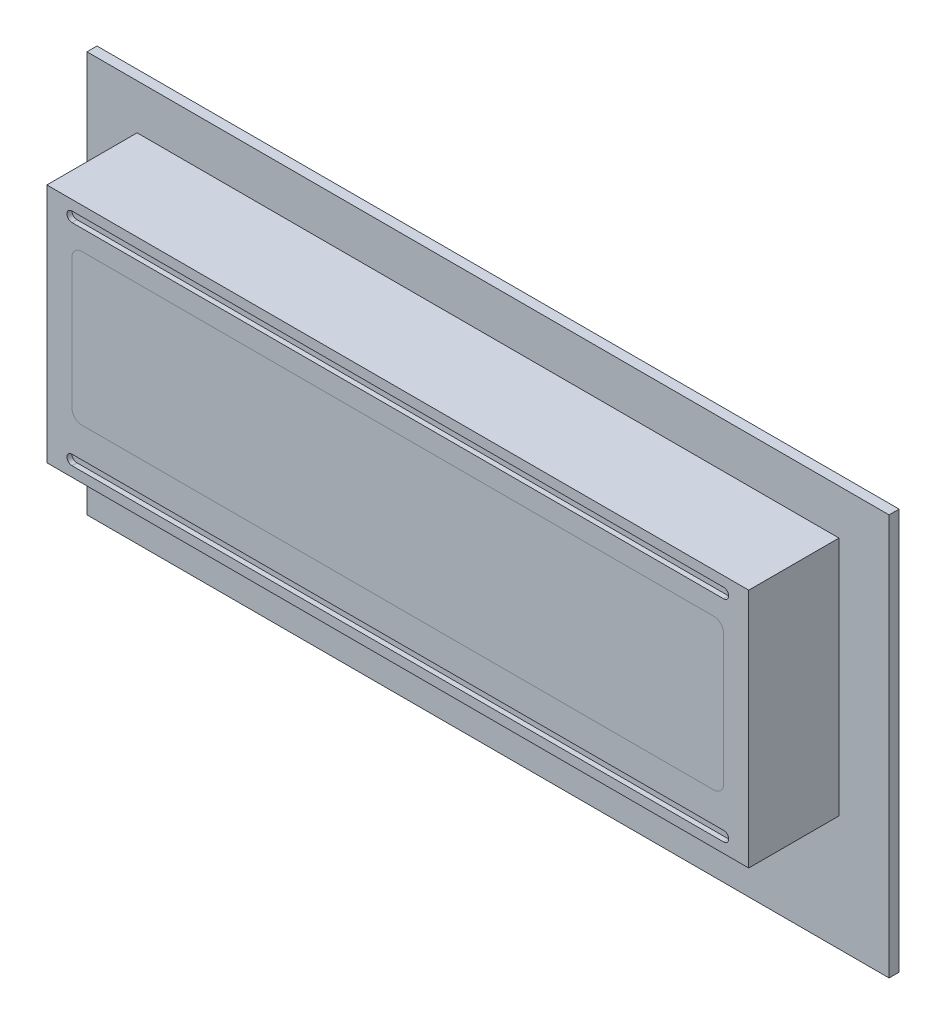
SolidWorks part; units mm, degrees
ref_plane "Plan de face" through (0, 0, 0) normal (0, 0, 1) x (1, 0, 0)
ref_plane "Plan de dessus" through (0, 0, 0) normal (0, 1, 0) x (1, 0, 0)
ref_plane "Plan de droite" through (0, 0, 0) normal (1, 0, 0) x (0, 0, -1)
sketch "Esquisse1" plane through (0, 0, 0) normal (0, 0, 1) x (1, 0, 0)
  line L0 (0, 30.9281) -> (0, -19.2371) construction
  line L1 (-46.5895, 0) -> (45.4509, 0) construction
  line L2 (-40, 20) -> (40, 20)
  line L3 (-40, 20) -> (-40, -20)
  line L4 (-40, -20) -> (40, -20)
  line L5 (40, 20) -> (40, -20)
  dimension "D1" = 80
  dimension "D2" = 40
extrude "Boss.-Extru.1" add sketch "Esquisse1" along normal blind 1
sketch "Esquisse2" plane through (0, 0, 1) normal (0, 0, 1) x (1, 0, 0)
  line L0 (0, -23.7129) -> (0, 24.4015) construction
  line L1 (-35, 15.5) -> (35, 15.5)
  line L2 (-35, 15.5) -> (-35, -8.5)
  line L3 (-35, -8.5) -> (35, -8.5)
  line L4 (35, 15.5) -> (35, -8.5)
  line L5 (-31.5, 11.5) -> (31.5, 11.5)
  line L6 (-32.5, 10.5) -> (-32.5, -2.5)
  line L7 (-31.5, -3.5) -> (31.5, -3.5)
  line L8 (32.5, 10.5) -> (32.5, -2.5)
  line L9 (40, 20) -> (-40, 20) construction
  arc A0 (31.5, -3.5) -> (32.5, -2.5) centre (31.5, -2.5) ccw
  arc A1 (31.5, 11.5) -> (32.5, 10.5) centre (31.5, 10.5) cw
  arc A2 (-32.5, -2.5) -> (-31.5, -3.5) centre (-31.5, -2.5) ccw
  arc A3 (-31.5, 11.5) -> (-32.5, 10.5) centre (-31.5, 10.5) ccw
  dimension "D7" = 1
  dimension "D1" = 70
  dimension "D2" = 24
  dimension "D3" = 4
  dimension "D4" = 15
  dimension "D5" = 65
  dimension "D6" = 4.5
extrude "Boss.-Extru.2" add sketch "Esquisse2" along normal blind 9
sketch "Esquisse3" plane through (0, 0, 10) normal (0, 0, 1) x (1, 0, 0)
  line L0 (0, -23.3686) -> (0, 26.295) construction
  line L2 (-32.5, 14.5) -> (32.5, 14.5)
  line L3 (-32.5, 13.2271) -> (-32.5, 14.6724) construction
  line L4 (-32.5, 13.5) -> (32.5, 13.5)
  line L5 (32.5, 13.1751) -> (32.5, 14.8249) construction
  line L6 (31.5, 11.5) -> (-31.5, 11.5) construction
  line L7 (-44.4775, 3.5) -> (44.11, 3.5) construction
  line L8 (35, 15.5) -> (-35, 15.5) construction
  line L9 (-35, -8.5) -> (35, -8.5) construction
  line L10 (32.5, -6.1751) -> (32.5, -7.8249) construction
  line L11 (-32.5, -6.2271) -> (-32.5, -7.6724) construction
  line L12 (-32.5, -6.5) -> (32.5, -6.5)
  line L13 (-32.5, -7.5) -> (32.5, -7.5)
  arc A0 (-32.5, 14.5) -> (-32.5, 13.5) centre (-32.5, 14) ccw
  arc A1 (32.5, 13.5) -> (32.5, 14.5) centre (32.5, 14) ccw
  arc A2 (32.5, -6.5) -> (32.5, -7.5) centre (32.5, -7) cw
  arc A3 (-32.5, -7.5) -> (-32.5, -6.5) centre (-32.5, -7) cw
  dimension "D1" = 65
  dimension "D2" = 1
  dimension "D3" = 2
extrude "Enlèv. mat.-Extru.1" cut sketch "Esquisse3" against normal blind 0.5
sketch "Esquisse4" plane through (0, 0, 10) normal (0, 0, 1) x (1, 0, 0)
  line L0 (32.5, -2.5) -> (32.5, 10.5) construction
  line L1 (-32.5, 10.5) -> (-32.5, -2.5) construction
  line L2 (-31.5, -3.5) -> (31.5, -3.5) construction
  line L3 (31.5, 11.5) -> (-31.5, 11.5) construction
  line L12 (32.5, -2.5) -> (32.5, 10.5)
  line L13 (-32.5, 10.5) -> (-32.5, -2.5)
  line L14 (-31.5, -3.5) -> (31.5, -3.5)
  line L15 (31.5, 11.5) -> (-31.5, 11.5)
  arc A0 (-31.5, 11.5) -> (-32.5, 10.5) centre (-31.5, 10.5) ccw construction
  arc A1 (-32.5, -2.5) -> (-31.5, -3.5) centre (-31.5, -2.5) ccw construction
  arc A2 (31.5, -3.5) -> (32.5, -2.5) centre (31.5, -2.5) ccw construction
  arc A3 (32.5, 10.5) -> (31.5, 11.5) centre (31.5, 10.5) ccw construction
  arc A4 (-31.5, 11.5) -> (-32.5, 10.5) centre (-31.5, 10.5) ccw
  arc A5 (-32.5, -2.5) -> (-31.5, -3.5) centre (-31.5, -2.5) ccw
  arc A6 (31.5, -3.5) -> (32.5, -2.5) centre (31.5, -2.5) ccw
  arc A7 (32.5, 10.5) -> (31.5, 11.5) centre (31.5, 10.5) ccw
extrude "Boss.-Extru.4" add sketch "Esquisse4" against normal blind 1 separate body
